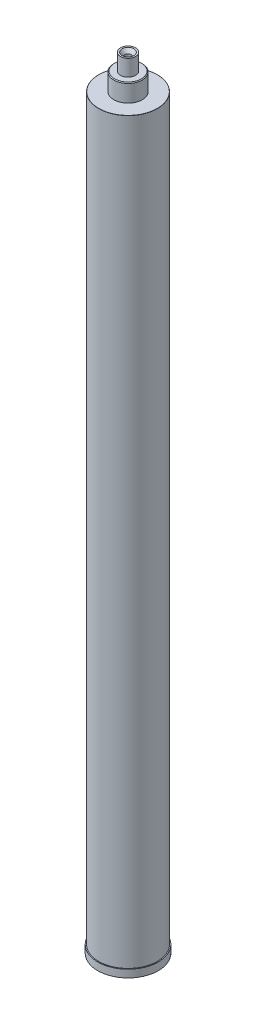
SolidWorks part; units mm, degrees
ref_plane "Front Plane" through (0, 0, 0) normal (0, 0, 1) x (1, 0, 0)
ref_plane "Top Plane" through (0, 0, 0) normal (0, 1, 0) x (1, 0, 0)
ref_plane "Right Plane" through (0, 0, 0) normal (1, 0, 0) x (0, 0, -1)
sketch "Sketch1" plane through (0, 0, 0) normal (0, 1, 0) x (1, 0, 0)
  circle A0 centre (0, 0) radius 49.2125
  dimension "D1" = 98.425
extrude "Boss-Extrude1" add sketch "Sketch1" along normal blind 1238.504
sketch "Sketch2" plane through (0, 0, 0) normal (0, 0, 1) x (1, 0, 0)
  line L0 (0, 1238.504) -> (0, 1295.654)
  line L1 (49.2125, 1238.504) -> (-49.2125, 1238.504) construction
  line L2 (0, 1295.654) -> (12.7, 1295.654)
  line L3 (12.7, 1295.654) -> (12.7, 1268.349)
  line L4 (12.7, 1268.349) -> (23.876, 1268.349)
  line L5 (23.876, 1268.349) -> (23.876, 1238.504)
  line L6 (23.876, 1238.504) -> (0, 1238.504)
  dimension "D1" = 57.15
  dimension "D2" = 23.876
  dimension "D3" = 29.845
  dimension "D4" = 12.7
revolve "Revolve1" add sketch "Sketch2" angle 360 about L0
sketch "Sketch3" plane through (0, 0, 0) normal (0, -1, 0) x (1, 0, 0)
  circle A0 centre (0, 0) radius 50.8
  dimension "D1" = 101.6
extrude "Boss-Extrude2" add sketch "Sketch3" along normal blind 12.7
chamfer "Chamfer1" distance 1.27 angle 45 1 edges at (0, 1268.349, -23.876)
fillet "Fillet1" radius 0.254 1 edges at (0, 1238.504, 49.2125)
hole_wizard "CSK for 3/8 Flat Head Socket Cap Screw1" positions "Sketch4" profile "Sketch5" countersink size "3/8" standard "ANSI Inch"
sketch "Sketch4" plane through (0, 1295.654, 0) normal (0, 1, 0) x (1, 0, 0)
  point P0 (0, 0)
sketch "Sketch5" plane through (0, 1295.654, 0) normal (1, 0, 0) x (0, 0, 1)
  line L0 (0, 0) -> (0, 28.3455)
  line L1 (0, 28.3455) -> (4.9022, 25.4)
  line L2 (4.9022, 25.4) -> (4.9022, 5.7708)
  line L3 (4.9022, 5.7708) -> (9.9187, 0)
  line L5 (9.9187, 0) -> (0, 0)
  line L6 (-4.9022, 5.7708) -> (-9.9187, 0) construction
  line L10 (0, 28.3455) -> (-4.9022, 25.4) construction
  line L11 (0, -6.35) -> (0, 107.95) construction
  dimension "Hole Dia." = 9.8044
  dimension "Hole Depth" = 25.4
  dimension "Near C'Sink Dia." = 19.8374
  dimension "Near C'Sink Angle" = 82
  dimension "Drill Angle" = 118
